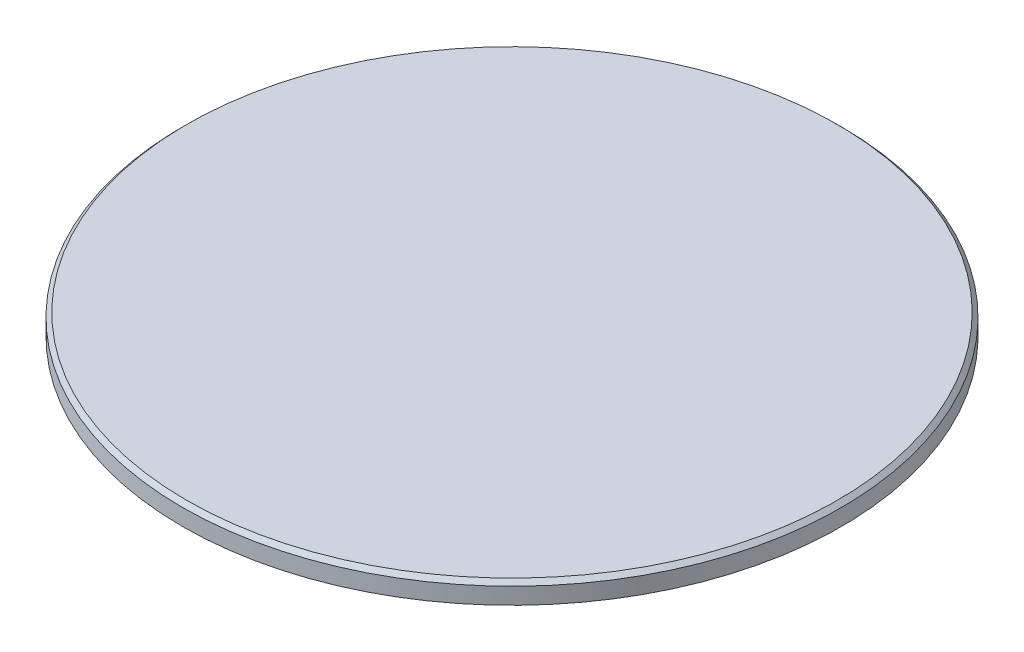
SolidWorks part; units mm, degrees
ref_plane "Front Plane" through (0, 0, 0) normal (0, 0, 1) x (1, 0, 0)
ref_plane "Top Plane" through (0, 0, 0) normal (0, 1, 0) x (1, 0, 0)
ref_plane "Right Plane" through (0, 0, 0) normal (1, 0, 0) x (0, 0, -1)
sketch "Sketch1" plane through (0, 0, 0) normal (0, 1, 0) x (1, 0, 0)
  circle A0 centre (0, 0) radius 15.95
  dimension "D1" = 31.9
extrude "Boss-Extrude1" add sketch "Sketch1" along normal blind 1
chamfer "Chamfer1" distance 0.2 angle 45 1 edges at (0, 1, 15.95)
